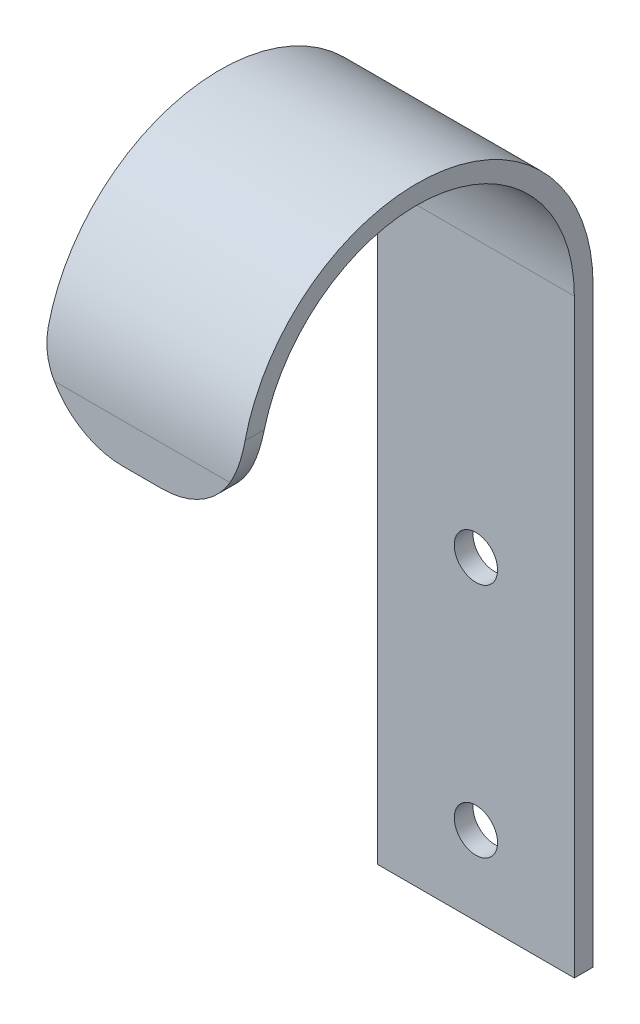
SolidWorks part; units mm, degrees
ref_plane "Front Plane" through (0, 0, 0) normal (0, 0, 1) x (1, 0, 0)
ref_plane "Top Plane" through (0, 0, 0) normal (0, 1, 0) x (1, 0, 0)
ref_plane "Right Plane" through (0, 0, 0) normal (1, 0, 0) x (0, 0, -1)
sketch "Sketch1" plane through (0, 0, 0) normal (1, 0, 0) x (0, 0, -1)
  line L0 (0, 0) -> (0, 75)
  line L1 (-40, 75) -> (-40, 70)
  line L2 (2.38, 0) -> (2.38, 75)
  line L3 (-42.38, 75) -> (-42.38, 70)
  line L4 (-40, 70) -> (-42.38, 70)
  line L5 (2.38, 0) -> (0, 0)
  arc A0 (0, 75) -> (-40, 75) centre (-20, 75) ccw
  arc A1 (2.38, 75) -> (-42.38, 75) centre (-20, 75) ccw
  dimension "D2" = 20
  dimension "D1" = 75
  dimension "D3" = 5
  dimension "D4" = 2.38
extrude "Boss-Extrude1" add sketch "Sketch1" along normal blind 25 contours A0 L1 L4 L3 A1 L2 L5 L0
fillet "Fillet1" radius 10 2 edges at (0, 70, 41.19) (25, 70, 41.19)
sketch "Sketch2" plane through (0, 0, 0) normal (0, 0, 1) x (1, 0, 0)
  line L0 (12.5, 0) -> (12.5, 70) construction
  line L1 (25, 0) -> (0, 0) construction
  line L2 (15, 70) -> (10, 70) construction
  circle A0 centre (12.5, 10) radius 2.75
  circle A1 centre (12.5, 40) radius 2.75
  dimension "D1" = 5.5
  dimension "D2" = 5.5
  dimension "D4" = 40
  dimension "D3" = 10
extrude "Cut-Extrude1" cut sketch "Sketch2" against normal blind 25
